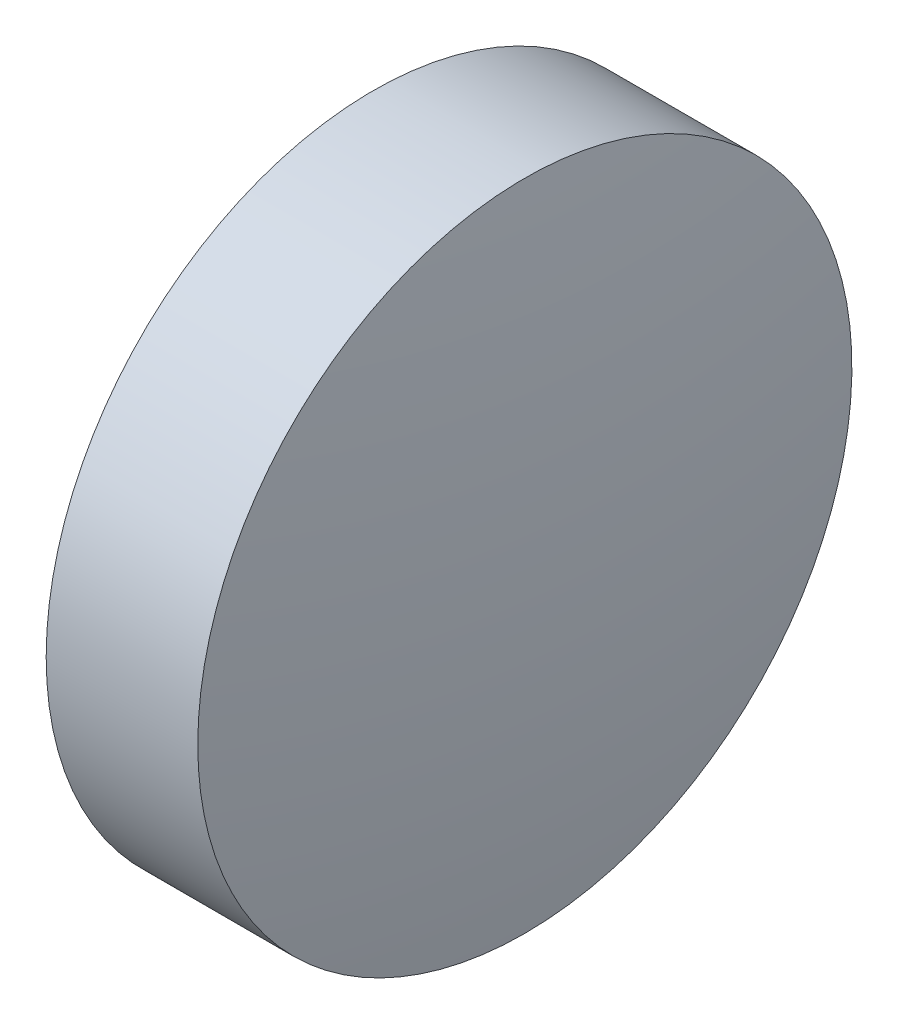
SolidWorks part; units mm, degrees
ref_plane "前视基准面" through (0, 0, 0) normal (0, 0, 1) x (1, 0, 0)
ref_plane "上视基准面" through (0, 0, 0) normal (0, 1, 0) x (1, 0, 0)
ref_plane "右视基准面" through (0, 0, 0) normal (1, 0, 0) x (0, 0, -1)
sketch "草图1" plane through (0, 0, 0) normal (0, 0, 1) x (1, 0, 0)
  line L0 (622.7258, 93.6314) -> (628.8612, 93.6314) construction
  line L1 (623.5874, 93.6314) -> (623.5874, 96.7814)
  line L2 (625.2874, 93.6314) -> (623.5874, 93.6314)
  line L5 (623.5874, 96.7814) -> (625.0474, 96.7814)
  arc A0 (625.2874, 93.6314) -> (625.0474, 96.7814) centre (604.4955, 93.6314) ccw
revolve "旋转1" add sketch "草图1" angle 360 about L0
